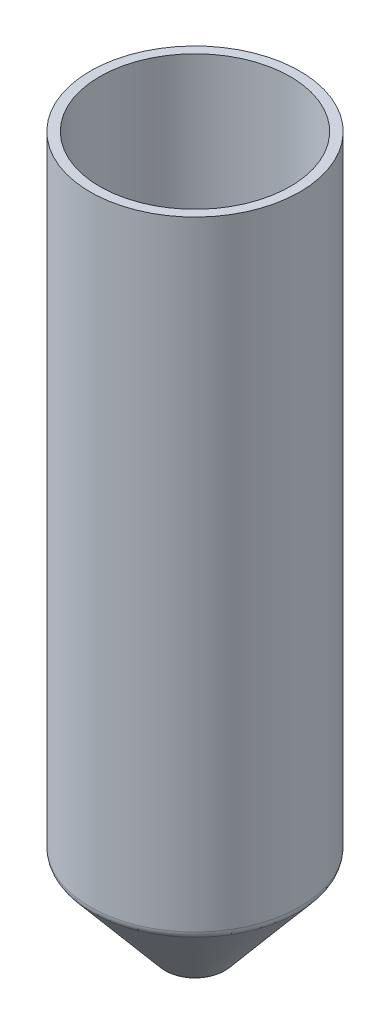
SolidWorks part; units mm, degrees
ref_plane "Front Plane" through (0, 0, 0) normal (0, 0, 1) x (1, 0, 0)
ref_plane "Top Plane" through (0, 0, 0) normal (0, 1, 0) x (1, 0, 0)
ref_plane "Right Plane" through (0, 0, 0) normal (1, 0, 0) x (0, 0, -1)
sketch "Sketch1" plane through (0, 0, 0) normal (0, 0, 1) x (1, 0, 0)
  line L0 (0, 0) -> (0, -17.2397) construction
  line L1 (-22, 0) -> (-22, -130.7279)
  line L2 (-20, 0) -> (-20, -130)
  line L3 (-20, -130) -> (-3.218, -150)
  line L4 (-22, -130.7279) -> (-5.8288, -150)
  line L5 (-3.218, -150) -> (-5.8288, -150)
  line L6 (-20, 0) -> (-22, 0)
  line L8 (-22, -130.7279) -> (-4.7501, -151.2856) construction
  dimension "D2" = 130
  dimension "D3" = 20
  dimension "D4" = 140
  dimension "D5" = 20
  dimension "D6" = 0
  dimension "D7" = 150
  dimension "D1" = 2
revolve "Revolve1" add sketch "Sketch1" angle 360 about L0
fillet "Fillet1" radius 2 1 edges at (-22, -130.7279, 0)
fillet "Fillet3" radius 2 1 edges at (-5.8288, -150, 0)
